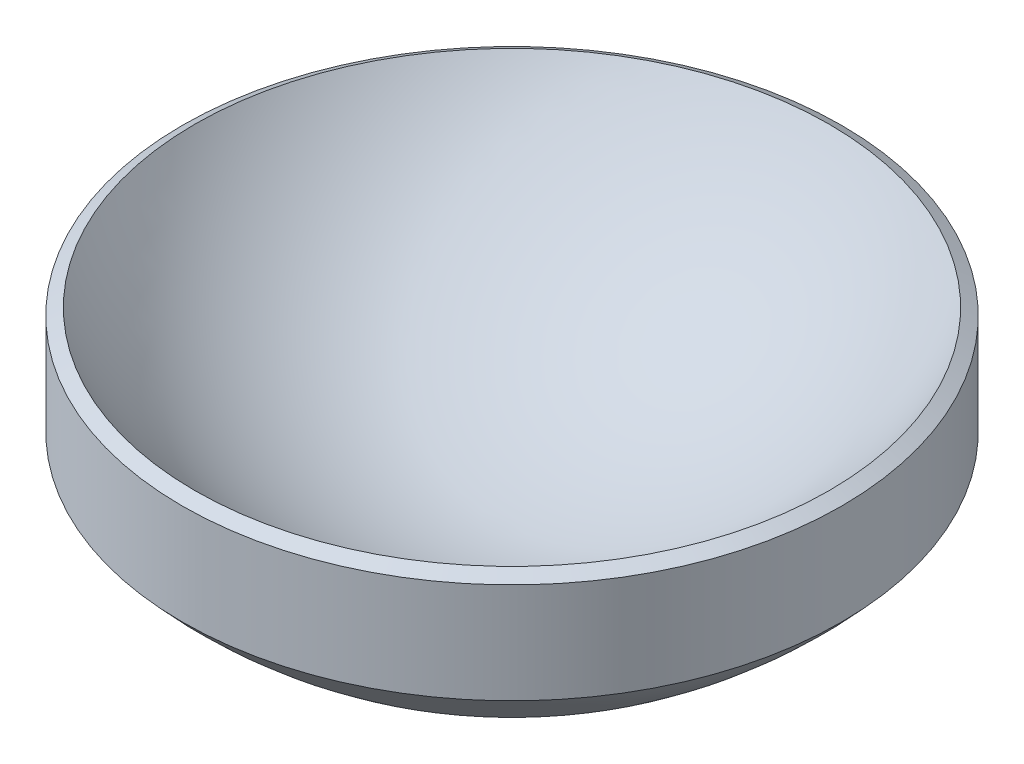
SolidWorks part; units mm, degrees
material "Медь"
ref_plane "Спереди" through (0, 0, 0) normal (0, 0, 1) x (1, 0, 0)
ref_plane "Сверху" through (0, 0, 0) normal (0, 1, 0) x (1, 0, 0)
ref_plane "Справа" through (0, 0, 0) normal (1, 0, 0) x (0, 0, -1)
sketch "Эскиз1" plane through (0, 0, 0) normal (0, 0, 1) x (1, 0, 0)
  line L0 (-5.1962, 2) -> (-4.3301, 2.5)
  line L1 (5.1962, 2) -> (4.3301, 2.5)
  line L2 (0, 0) -> (0, -1) construction
  arc A0 (-4.3301, 2.5) -> (4.3301, 2.5) centre (0, 5) ccw
  arc A1 (-5.1962, 2) -> (5.1962, 2) centre (0, 5) ccw
  dimension "D1" = 5
  dimension "D2" = 2.5
  dimension "D3" = 1
revolve "Повернуть1" add sketch "Эскиз1" angle 360 about L2
sketch "Эскиз2" plane through (0, 0, 0) normal (0, 0, 1) x (1, 0, 0)
  line L0 (-4.5, 4.0654) -> (-4.5, -1.2279)
  line L1 (-4.5, -1.2279) -> (-6.4027, -1.2279)
  line L2 (-6.4027, -1.2279) -> (-6.4027, 4.0654)
  line L3 (-6.4027, 4.0654) -> (-4.5, 4.0654)
  line L4 (0, 0) -> (0, 2.5) construction
  line L5 (-4.3301, 2.5) -> (4.3301, 2.5) construction
  dimension "D1" = 9
revolve "Вырез-Повернуть1" cut sketch "Эскиз2" angle 360 about L4
sketch "Эскиз3" plane through (0, 0, 0) normal (0, 0, 1) x (1, 0, 0)
  line L1 (-6.125, -0.7) -> (5.779, -0.7)
  line L2 (-6.125, -0.7) -> (-6.125, -3.1032)
  line L3 (-6.125, -3.1032) -> (5.779, -3.1032)
  line L4 (5.779, -0.7) -> (5.779, -3.1032)
  dimension "D1" = 0.7
extrude "Вырез-Вытянуть1" cut sketch "Эскиз3" against normal through all and the other way through all
